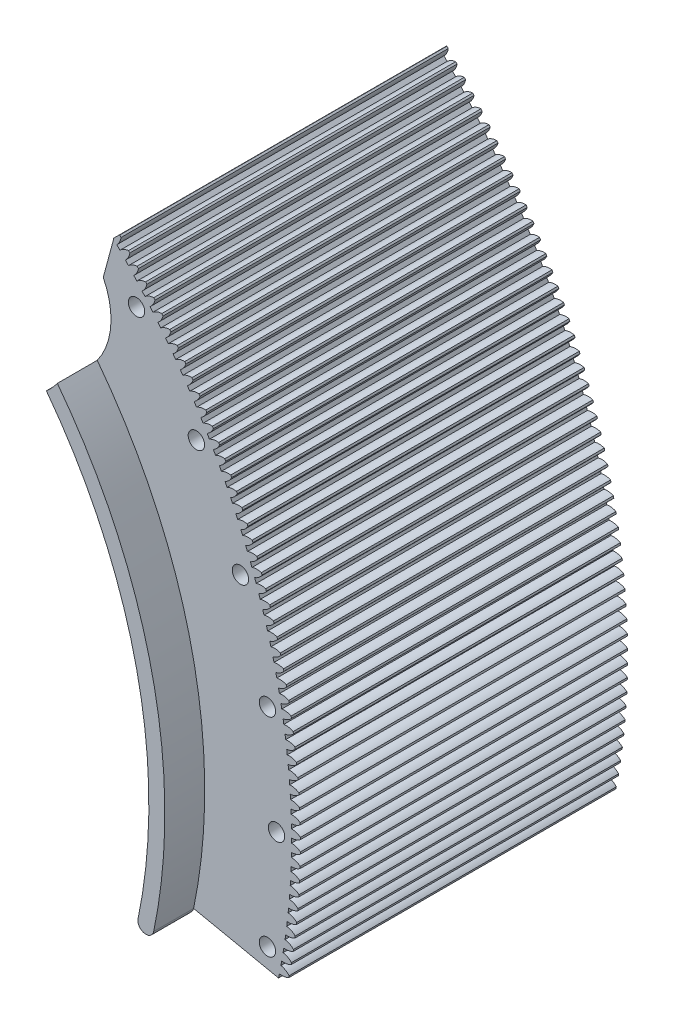
SolidWorks part; units mm, degrees
material "ABS"
ref_plane "Front Plane" through (0, 0, 0) normal (0, 0, 1) x (1, 0, 0)
ref_plane "Top Plane" through (0, 0, 0) normal (0, 1, 0) x (1, 0, 0)
ref_plane "Right Plane" through (0, 0, 0) normal (1, 0, 0) x (0, 0, -1)
sketch "Sketch1" plane through (0, 0, 0) normal (0, 0, 1) x (1, 0, 0)
  line L0 (0, 0) -> (203.2, 0) construction
  line L1 (203.2, 0) -> (209.55, 0) construction
  line L2 (148.1742, 148.1742) -> (143.6841, 143.6841) construction
  line L3 (143.6841, 143.6841) -> (0, 0) construction
  line L4 (203.2, 0) -> (203.2, -50.8) construction
  line L5 (198.9038, -41.5636) -> (205.1195, -42.8625) construction
  line L6 (198.9038, -41.5636) -> (0, 0) construction
  line L7 (203.2, -50.8) -> (205.829, -50.8) construction
  line L8 (160.5177, 124.5966) -> (165.5338, 128.4903) construction
  line L9 (160.5177, 124.5966) -> (0, 0) construction
  arc A0 (203.2, 0) -> (160.5177, 124.5966) centre (0, 0) ccw
  arc A1 (209.55, 0) -> (165.5338, 128.4903) centre (0, 0) ccw
  arc A2 (203.2, 0) -> (198.9038, -41.5636) centre (0, 0) cw
  arc A3 (198.9038, -41.5636) -> (205.1195, -42.8625) centre (202.0116, -42.2131) ccw
  arc A4 (205.1195, -42.8625) -> (209.55, 0) centre (0, 0) ccw
  arc A5 (160.5177, 124.5966) -> (165.5338, 128.4903) centre (163.0257, 126.5435) cw
  arc A6 (160.5177, 124.5966) -> (143.6841, 143.6841) centre (0, 0) ccw construction
  arc A7 (165.5338, 128.4903) -> (148.1742, 148.1742) centre (0, 0) ccw construction
  dimension "D1" = 203.2
  dimension "D2" = 45
  dimension "D3" = 6.35
  dimension "D4" = 50.8
  dimension "D5" = 7.9375
  dimension "D6" = 25.4
extrude "Boss-Extrude2" add sketch "Sketch1" along normal blind 15.875 contours A5 A0 A2 A3 A4 A1
sketch "Sketch3" plane through (0, 0, 15.875) normal (0, 0, 1) x (1, 0, 0)
  line L0 (0, 0) -> (238.125, 0) construction
  line L1 (0, 0) -> (238.125, 0) construction
  line L2 (0, 0) -> (234.5073, 41.35) construction
  line L3 (0, 0) -> (238.125, 0) construction
  line L4 (0, 0) -> (234.5073, -41.35) construction
  line L5 (160.5177, 124.5966) -> (193.1228, 149.9053) construction
  line L6 (160.5177, 124.5966) -> (0, 0) construction
  line L7 (198.9038, -41.5636) -> (239.3061, -50.0062)
  line L8 (198.9038, -41.5636) -> (0, 0) construction
  line L9 (160.5177, 124.5966) -> (173.4144, 172.3237)
  line L10 (0, 0) -> (173.4144, 172.3237) construction
  circle A0 centre (238.125, 0) radius 3.2639
  circle A1 centre (234.5073, 41.35) radius 3.2639
  circle A2 centre (223.7643, 81.4435) radius 3.2639
  circle A3 centre (206.2223, 119.0625) radius 3.2639
  circle A4 centre (182.4143, 153.0638) radius 3.2639
  circle A5 centre (234.5073, -41.35) radius 3.2639
  arc A6 (198.9038, -41.5636) -> (160.5177, 124.5966) centre (0, 0) ccw construction
  arc A7 (198.9038, -41.5636) -> (160.5177, 124.5966) centre (0, 0) ccw
  arc A8 (193.1228, 149.9053) -> (239.3061, -50.0062) centre (0, 0) cw
  arc A9 (193.1228, 149.9053) -> (173.4144, 172.3237) centre (0, 0) ccw
  dimension "D2" = 6.5278
  dimension "D7" = 244.475
  dimension "D8" = 7
  dimension "D1" = 238.125
  dimension "D4" = 10
  dimension "D6" = 10
  dimension "D3" = 5
  dimension "D5" = 2
extrude "Boss-Extrude3" add sketch "Sketch3" along normal blind 130.175
ref_plane "Plane1" through (0, 0, 80.9625) normal (0, 0, -1) x (-1, 0, 0)
mirror "Mirror1" about plane through (0, 0, 80.9625) normal (0, 0, -1) of "Boss-Extrude2"
sketch "Sketch4" plane through (0, 0, 146.05) normal (0, 0, 1) x (1, 0, 0)
  line L0 (0, 0) -> (42.777, 0) construction
  line L1 (0, 0) -> (143.6841, 143.6841) construction
  circle A0 centre (143.6841, 143.6841) radius 28.575
  dimension "D3" = 57.15
  dimension "D1" = 45
  dimension "D2" = 203.2
extrude "Cut-Extrude1" cut sketch "Sketch4" against normal through all both and the other way through all
sketch "Sketch5" plane through (0, 0, 146.05) normal (0, 0, 1) x (1, 0, 0)
  line L0 (0, 0) -> (242.414, -50.6557) construction
  line L1 (205.1195, -42.8625) -> (239.3061, -50.0062) construction
  line L2 (0, 0) -> (175.6666, 174.5617) construction
  line L3 (173.1329, 172.044) -> (175.6666, 174.5617)
  line L4 (238.9176, -49.9251) -> (242.414, -50.6557)
  circle A0 centre (0, 0) radius 246.0625 construction
  arc A1 (242.414, -50.6557) -> (175.6666, 174.5617) centre (0, 0) ccw
  arc A2 (238.9176, -49.9251) -> (173.1329, 172.044) centre (0, 0) ccw
  dimension "D1" = 492.125
  dimension "D2" = 247.65
  dimension "D3" = 3.5719
extrude "Boss-Extrude4" add sketch "Sketch5" against normal up to surface (130.175 mm away) up to face at (200.8941, 75.0138, 15.875)
sketch "Sketch6" plane through (0, 0, 146.05) normal (0, 0, 1) x (1, 0, 0)
  line L0 (0, 0) -> (247.65, 0) construction
  line L1 (246.0593, 1.2468) -> (246.0593, -1.2468) construction
  line L2 (0, 0) -> (248.431, -2.5177) construction
  line L3 (246.0593, -1.2468) -> (246.0341, -3.7403) construction
  line L4 (0, 0) -> (244.0765, 0.8934) construction
  line L5 (242.6337, 0) -> (261.6529, 6.9224) construction
  arc A0 (242.414, -50.6557) -> (175.6666, 174.5617) centre (0, 0) ccw construction
  arc A1 (248.4274, 2.8517) -> (244.0765, 0.8934) centre (244.055, 6.7536) cw
  arc A2 (238.9176, -49.9251) -> (173.1329, 172.044) centre (0, 0) ccw construction
  arc A3 (244.0765, -0.8934) -> (244.0765, 0.8934) centre (0, 0) ccw
  arc A4 (248.4274, -2.8517) -> (244.0765, -0.8934) centre (244.055, -6.7536) ccw
  arc A5 (248.4274, -2.8517) -> (248.4274, 2.8517) centre (0, 0) ccw
  arc A6 (242.414, -50.6557) -> (175.6666, 174.5617) centre (0, 0) ccw construction
  circle A7 centre (0, 0) radius 246.0625 construction
  point P0 (246.0467, -2.4936)
  point P25 (238.9176, 0)
  dimension "D1" = 0.7937
  dimension "D2" = 20
  dimension "D3" = 0.581
extrude "Cut-Extrude2" cut sketch "Sketch6" against normal through all
pattern_circular "CirPattern1" count 310 over 360 about axis through (0, 0, 0) along (0, 0, 1) of "Cut-Extrude2"
sketch "Sketch8" plane through (0, 0, 146.05) normal (0, 0, 1) x (1, 0, 0)
  circle A0 centre (0, 0) radius 246.0625
  dimension "D1" = 492.125
equation "\"Module\" = .0625in"
equation "\"Number of Teeth\"= 310"
equation "\"D1@Sketch5\"=\"Module\" * \"Number of Teeth\""
equation "\"D2@Sketch5\"=((\"Number of Teeth\" + 2) * \"Module\")/2"
equation "\"D3@Sketch5\"=2.25 * \"Module\""
equation "\"D3@Sketch6\"=180/\"Number of Teeth\""
equation "\"D1@CirPattern1\"=\"Number of Teeth\""
equation "\"D1@Sketch8\"=\"Module\" * \"Number of Teeth\""
